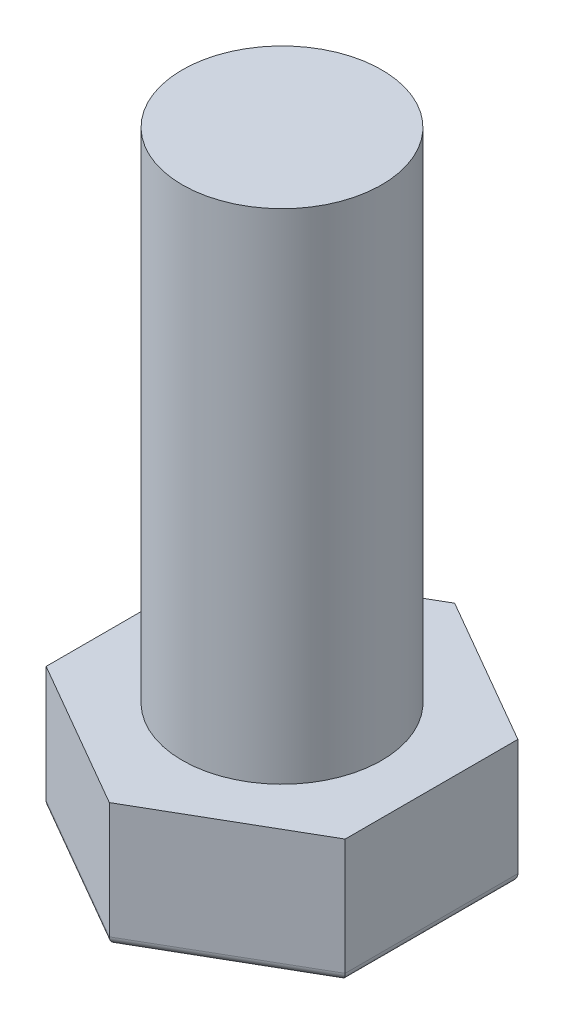
SolidWorks part; units mm, degrees
material "純碳鋼"
ref_plane "前基準面" through (0, 0, 0) normal (0, 0, 1) x (1, 0, 0)
ref_plane "上基準面" through (0, 0, 0) normal (0, 1, 0) x (1, 0, 0)
ref_plane "右基準面" through (0, 0, 0) normal (1, 0, 0) x (0, 0, -1)
sketch "草圖1" plane through (0, 0, 0) normal (0, 1, 0) x (1, 0, 0)
  line L1 (18, -10.3923) -> (18, 10.3923)
  line L2 (18, 10.3923) -> (0, 20.7846)
  line L3 (0, 20.7846) -> (-18, 10.3923)
  line L4 (-18, 10.3923) -> (-18, -10.3923)
  line L5 (-18, -10.3923) -> (0, -20.7846)
  line L6 (0, -20.7846) -> (18, -10.3923)
  circle A0 centre (0, 0) radius 18 construction
  dimension "D1" = 36
extrude "填料-伸長1" add sketch "草圖1" along normal blind 15 contours L3 L4 L5 L6 L1 L2
sketch "草圖2" plane through (0, 15, 0) normal (0, 1, 0) x (1, 0, 0)
  circle A0 centre (0, 0) radius 12
  dimension "D1" = 24
extrude "填料-伸長2" add sketch "草圖2" along normal blind 60 contours A0
fillet "圓角1" radius 1 6 edges at (-9, 0, -15.5885) (-18, 0, 0) (-9, 0, 15.5885) (9, 0, 15.5885) (18, 0, 0) (9, 0, -15.5885)
sketch3d "URDF Reference"
  line L0 (0, 0, 0) -> (13.2953, 0, 0.1328) construction
  line L1 (0, 0, 0) -> (0, 0, -10) construction
  point P0 (0, 0, 0)
  point P1 (0, 0, 0)
  point P6 (13.2953, 0, 0.1328)
